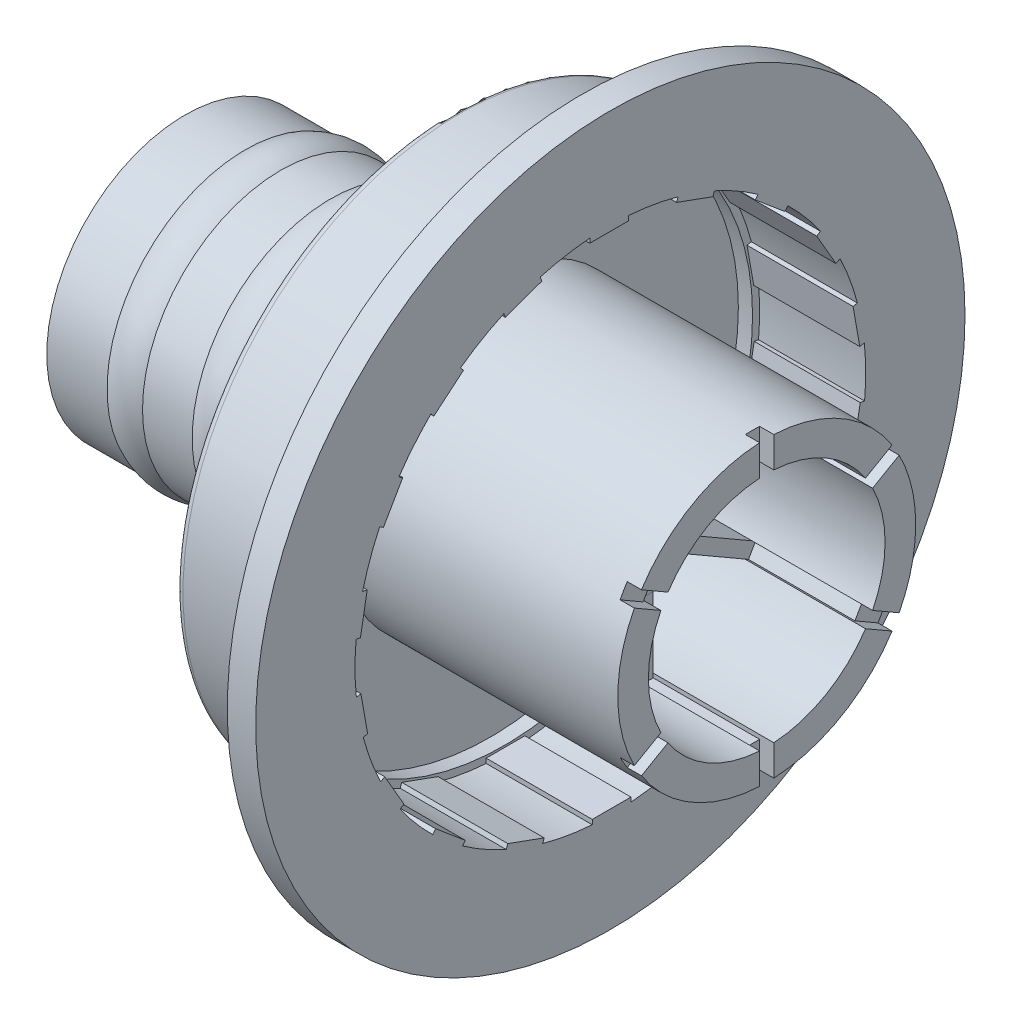
SolidWorks part; units mm, degrees
material "PE High Density"
ref_plane "Front Plane" through (0, 0, 0) normal (0, 0, 1) x (1, 0, 0)
ref_plane "Top Plane" through (0, 0, 0) normal (0, 1, 0) x (1, 0, 0)
ref_plane "Right Plane" through (0, 0, 0) normal (1, 0, 0) x (0, 0, -1)
sketch "Sketch1" plane through (0, 0, 0) normal (0, 0, 1) x (1, 0, 0)
  line L0 (-11.1655, 0) -> (0, 0) construction
  line L2 (0, 5.334) -> (9.906, 5.334)
  line L6 (5.5998, 12.7) -> (6.6158, 12.7)
  line L7 (6.6158, 12.7) -> (6.6158, 9.906)
  line L8 (6.6158, 9.906) -> (11.2522, 9.906)
  line L9 (11.2522, 9.906) -> (11.2522, 4.953)
  line L10 (11.2522, 4.953) -> (20.828, 4.953)
  line L13 (5.5998, 12.7) -> (5.5998, 9.144)
  line L14 (5.5998, 9.144) -> (9.906, 9.144)
  line L15 (9.906, 9.144) -> (9.906, 5.334)
  line L16 (0, 5.334) -> (0, 4.2378)
  line L17 (0, 4.2378) -> (6.35, 4.2378)
  line L18 (0, 0) -> (28.3483, 0) construction
  line L19 (6.35, 4.2378) -> (6.35, 0.4603)
  line L20 (6.35, 0.4603) -> (7.5692, 0.4603)
  line L21 (7.5692, 0.4603) -> (7.5692, 4.191)
  line L22 (7.5692, 4.191) -> (20.828, 4.191)
  line L23 (20.828, 4.191) -> (20.828, 4.953)
  point P1 (0, 4.7859)
  point P5 (6.1078, 12.7)
  dimension "D1" = 10.668
  dimension "D2" = 9.906
  dimension "D3" = 25.4
  dimension "D4" = 3.556
  dimension "D5" = 9.906
  dimension "D6" = 1.016
  dimension "D7" = 0.762
  dimension "D8" = 6.35
  dimension "D9" = 9.5758
  dimension "D10" = 13.2588
  dimension "D11" = 20.828
  dimension "D12" = 0.762
revolve "Revolve2" add sketch "Sketch1" angle 360 about L0
fillet "Fillet1" radius 0.254 1 edges at (11.2522, 0, 9.906)
sketch "Sketch3" plane through (0, 0, 0) normal (0, 0, 1) x (1, 0, 0)
  line L0 (-9.4589, 0) -> (27.8248, 0) construction
  line L1 (18.669, 4.953) -> (17.399, 4.953)
  line L2 (20.828, -4.953) -> (20.828, 4.953) construction
  line L3 (15.621, 4.953) -> (14.351, 4.953)
  arc A0 (17.399, 4.953) -> (18.669, 4.953) centre (18.034, 3.6026) cw
  arc A1 (14.351, 4.953) -> (15.621, 4.953) centre (14.986, 3.6026) cw
  dimension "D1" = 9.906
  dimension "D2" = 2.159
  dimension "D3" = 1.27
  dimension "D4" = 2
revolve "Revolve3" add sketch "Sketch3" angle 360 about L0
sketch "Sketch6" plane through (9.906, 0, 0) normal (-1, 0, 0) x (0, 0, 1)
  line L0 (-0.7374, 9.144) -> (0.6478, 9.144)
  line L1 (0.6478, 9.144) -> (0.6478, 8.9554)
  line L2 (0.6478, 8.9554) -> (-0.7374, 8.9554)
  line L3 (-0.7374, 8.9554) -> (-0.7374, 9.144)
  line L4 (3.6717, 8.1937) -> (2.37, 8.6675)
  line L5 (2.37, 8.6675) -> (2.4345, 8.8448)
  line L6 (3.7362, 8.371) -> (3.6717, 8.1937)
  line L7 (2.4345, 8.8448) -> (3.7362, 8.371)
  line L8 (6.2527, 6.4438) -> (5.1915, 7.3342)
  line L9 (5.1915, 7.3342) -> (5.3127, 7.4787)
  line L10 (6.3739, 6.5883) -> (6.2527, 6.4438)
  line L11 (5.3127, 7.4787) -> (6.3739, 6.5883)
  line L12 (8.0795, 3.9167) -> (7.3869, 5.1163)
  line L13 (7.3869, 5.1163) -> (7.5502, 5.2106)
  line L14 (8.2428, 4.011) -> (8.0795, 3.9167)
  line L15 (7.5502, 5.2106) -> (8.2428, 4.011)
  line L16 (8.9318, 0.9171) -> (8.6913, 2.2813)
  line L17 (8.6913, 2.2813) -> (8.877, 2.3141)
  line L18 (9.1176, 0.9499) -> (8.9318, 0.9171)
  line L19 (8.877, 2.3141) -> (9.1176, 0.9499)
  line L20 (8.7068, -2.1931) -> (8.9474, -0.8289)
  line L21 (8.9474, -0.8289) -> (9.1331, -0.8616)
  line L22 (8.8926, -2.2258) -> (8.7068, -2.1931)
  line L23 (9.1331, -0.8616) -> (8.8926, -2.2258)
  line L24 (7.4317, -5.0387) -> (8.1243, -3.839)
  line L25 (8.1243, -3.839) -> (8.2877, -3.9334)
  line L26 (7.595, -5.133) -> (7.4317, -5.0387)
  line L27 (8.2877, -3.9334) -> (7.595, -5.133)
  line L28 (5.2601, -7.2766) -> (6.3213, -6.3862)
  line L29 (6.3213, -6.3862) -> (6.4426, -6.5307)
  line L30 (5.3814, -7.4211) -> (5.2601, -7.2766)
  line L31 (6.4426, -6.5307) -> (5.3814, -7.4211)
  line L32 (2.4542, -8.6369) -> (3.7559, -8.1631)
  line L33 (3.7559, -8.1631) -> (3.8204, -8.3403)
  line L34 (2.5187, -8.8141) -> (2.4542, -8.6369)
  line L35 (3.8204, -8.3403) -> (2.5187, -8.8141)
  line L36 (-0.6478, -8.9554) -> (0.7374, -8.9554)
  line L37 (0.7374, -8.9554) -> (0.7374, -9.144)
  line L38 (-0.6478, -9.144) -> (-0.6478, -8.9554)
  line L39 (0.7374, -9.144) -> (-0.6478, -9.144)
  line L40 (-3.6717, -8.1937) -> (-2.37, -8.6675)
  line L41 (-2.37, -8.6675) -> (-2.4345, -8.8448)
  line L42 (-3.7362, -8.371) -> (-3.6717, -8.1937)
  line L43 (-2.4345, -8.8448) -> (-3.7362, -8.371)
  line L44 (-6.2527, -6.4438) -> (-5.1915, -7.3342)
  line L45 (-5.1915, -7.3342) -> (-5.3127, -7.4787)
  line L46 (-6.3739, -6.5883) -> (-6.2527, -6.4438)
  line L47 (-5.3127, -7.4787) -> (-6.3739, -6.5883)
  line L48 (-8.0795, -3.9167) -> (-7.3869, -5.1163)
  line L49 (-7.3869, -5.1163) -> (-7.5502, -5.2106)
  line L50 (-8.2428, -4.011) -> (-8.0795, -3.9167)
  line L51 (-7.5502, -5.2106) -> (-8.2428, -4.011)
  line L52 (-8.9318, -0.9171) -> (-8.6913, -2.2813)
  line L53 (-8.6913, -2.2813) -> (-8.877, -2.3141)
  line L54 (-9.1176, -0.9499) -> (-8.9318, -0.9171)
  line L55 (-8.877, -2.3141) -> (-9.1176, -0.9499)
  line L56 (-8.7068, 2.1931) -> (-8.9474, 0.8289)
  line L57 (-8.9474, 0.8289) -> (-9.1331, 0.8616)
  line L58 (-8.8926, 2.2258) -> (-8.7068, 2.1931)
  line L59 (-9.1331, 0.8616) -> (-8.8926, 2.2258)
  line L60 (-7.4317, 5.0387) -> (-8.1243, 3.839)
  line L61 (-8.1243, 3.839) -> (-8.2877, 3.9334)
  line L62 (-7.595, 5.133) -> (-7.4317, 5.0387)
  line L63 (-8.2877, 3.9334) -> (-7.595, 5.133)
  line L64 (-5.2601, 7.2766) -> (-6.3213, 6.3862)
  line L65 (-6.3213, 6.3862) -> (-6.4426, 6.5307)
  line L66 (-5.3814, 7.4211) -> (-5.2601, 7.2766)
  line L67 (-6.4426, 6.5307) -> (-5.3814, 7.4211)
  line L68 (-2.4542, 8.6369) -> (-3.7559, 8.1631)
  line L69 (-3.7559, 8.1631) -> (-3.8204, 8.3403)
  line L70 (-2.5187, 8.8141) -> (-2.4542, 8.6369)
  line L71 (-3.8204, 8.3403) -> (-2.5187, 8.8141)
  point P75 (0, 0)
  dimension "D1" = 1.3853
  dimension "D2" = 0.1886
  dimension "D3" = 18
extrude "Boss-Extrude2" add sketch "Sketch6" along normal up to surface (4.3062 mm away) up to face at (5.5998, 0, 9.144)
sketch "Sketch9" plane through (9.906, 0, 0) normal (-1, 0, 0) x (0, 0, 1)
  circle A0 centre (0, 0) radius 9.144 construction
  circle A1 centre (0, 0) radius 9.144
  circle A2 centre (0, 0) radius 8.89
  dimension "D1" = 0.254
extrude "Boss-Extrude3" add sketch "Sketch9" along normal blind 0.508
sketch "Sketch12" plane through (0, 0, 0) normal (0, 0, 1) x (1, 0, 0)
  line L0 (6.35, 0.9358) -> (6.35, 4.2378)
  line L1 (6.35, 4.2378) -> (4.318, 4.2378)
  line L2 (6.35, 4.2378) -> (0, 4.2378) construction
  line L3 (4.318, 4.2378) -> (4.318, 1.6978)
  line L4 (5.08, 0.9358) -> (6.35, 0.9358)
  arc A0 (4.318, 1.6978) -> (5.08, 0.9358) centre (5.08, 1.6978) ccw
  dimension "D1" = 2.032
  dimension "D2" = 2.54
  dimension "D3" = 3.302
extrude "Boss-Extrude5" add sketch "Sketch12" along normal mid plane 0.508
pattern_circular "CirPattern1" count 6 over 360 about axis through (0, 0, 0) along (1, 0, 0) of "Boss-Extrude5"
sketch "Sketch13" plane through (0, 0, 0) normal (-1, 0, 0) x (0, 0, 1)
  line L0 (-0.254, 0.9358) -> (-0.254, 4.2301) construction
  line L1 (-0.254, 4.0563) -> (0.254, 4.0563)
  line L2 (-0.254, 4.0563) -> (-0.254, 4.3783)
  line L3 (-0.254, 4.3783) -> (0.254, 4.3783)
  line L4 (0.254, 4.0563) -> (0.254, 4.3783)
  line L5 (-0.254, 4.0563) -> (0.254, 4.3783) construction
  line L6 (-0.254, 4.3783) -> (0.254, 4.0563) construction
  line L7 (3.3859, 2.2481) -> (3.9187, 1.9692) construction
  line L8 (3.6647, 2.4091) -> (3.6399, 1.8082) construction
  line L9 (3.3859, 2.2481) -> (3.6647, 2.4091)
  line L10 (3.3859, 2.2481) -> (3.6399, 1.8082)
  line L11 (3.6399, 1.8082) -> (3.9187, 1.9692)
  line L12 (3.6647, 2.4091) -> (3.9187, 1.9692)
  line L13 (3.6399, -1.8082) -> (3.6647, -2.4091) construction
  line L14 (3.9187, -1.9692) -> (3.3859, -2.2481) construction
  line L15 (3.6399, -1.8082) -> (3.9187, -1.9692)
  line L16 (3.6399, -1.8082) -> (3.3859, -2.2481)
  line L17 (3.3859, -2.2481) -> (3.6647, -2.4091)
  line L18 (3.9187, -1.9692) -> (3.6647, -2.4091)
  line L19 (0.254, -4.0563) -> (-0.254, -4.3783) construction
  line L20 (0.254, -4.3783) -> (-0.254, -4.0563) construction
  line L21 (0.254, -4.0563) -> (0.254, -4.3783)
  line L22 (0.254, -4.0563) -> (-0.254, -4.0563)
  line L23 (-0.254, -4.0563) -> (-0.254, -4.3783)
  line L24 (0.254, -4.3783) -> (-0.254, -4.3783)
  line L25 (-3.3859, -2.2481) -> (-3.9187, -1.9692) construction
  line L26 (-3.6647, -2.4091) -> (-3.6399, -1.8082) construction
  line L27 (-3.3859, -2.2481) -> (-3.6647, -2.4091)
  line L28 (-3.3859, -2.2481) -> (-3.6399, -1.8082)
  line L29 (-3.6399, -1.8082) -> (-3.9187, -1.9692)
  line L30 (-3.6647, -2.4091) -> (-3.9187, -1.9692)
  line L31 (-3.6399, 1.8082) -> (-3.6647, 2.4091) construction
  line L32 (-3.9187, 1.9692) -> (-3.3859, 2.2481) construction
  line L33 (-3.6399, 1.8082) -> (-3.9187, 1.9692)
  line L34 (-3.6399, 1.8082) -> (-3.3859, 2.2481)
  line L35 (-3.3859, 2.2481) -> (-3.6647, 2.4091)
  line L36 (-3.9187, 1.9692) -> (-3.6647, 2.4091)
  point P4 (0, 4.2173)
  point P14 (3.6523, 2.1087)
  point P19 (3.6523, -2.1087)
  point P24 (0, -4.2173)
  point P29 (-3.6523, -2.1087)
  point P34 (-3.6523, 2.1087)
  point P35 (0, 0)
  dimension "D1" = 6
extrude "Cut-Extrude1" cut sketch "Sketch13" against normal up to vertex (4.318 mm away)
sketch "Sketch15" plane through (0, 0, 0) normal (-1, 0, 0) x (0, 0, 1)
  line L0 (3.5364, 2.335) -> (4.8524, 2.5082) construction
  line L1 (-0.254, 4.2301) -> (0.254, 4.2301)
  line L2 (-0.254, 4.2301) -> (-0.254, 5.4564)
  line L3 (-0.254, 5.4564) -> (0.254, 5.4564)
  line L4 (0.254, 4.2301) -> (0.254, 5.4564)
  line L5 (-0.254, 4.2301) -> (0.254, 5.4564) construction
  line L6 (-0.254, 5.4564) -> (0.254, 4.2301) construction
  line L7 (4.5984, 2.9482) -> (3.7904, 1.8951) construction
  line L8 (3.5364, 2.335) -> (4.5984, 2.9482)
  line L9 (3.5364, 2.335) -> (3.7904, 1.8951)
  line L10 (3.7904, 1.8951) -> (4.8524, 2.5082)
  line L11 (4.5984, 2.9482) -> (4.8524, 2.5082)
  line L12 (3.7904, -1.8951) -> (4.5984, -2.9482) construction
  line L13 (4.8524, -2.5082) -> (3.5364, -2.335) construction
  line L14 (3.7904, -1.8951) -> (4.8524, -2.5082)
  line L15 (3.7904, -1.8951) -> (3.5364, -2.335)
  line L16 (3.5364, -2.335) -> (4.5984, -2.9482)
  line L17 (4.8524, -2.5082) -> (4.5984, -2.9482)
  line L18 (0.254, -4.2301) -> (-0.254, -5.4564) construction
  line L19 (0.254, -5.4564) -> (-0.254, -4.2301) construction
  line L20 (0.254, -4.2301) -> (0.254, -5.4564)
  line L21 (0.254, -4.2301) -> (-0.254, -4.2301)
  line L22 (-0.254, -4.2301) -> (-0.254, -5.4564)
  line L23 (0.254, -5.4564) -> (-0.254, -5.4564)
  line L24 (-3.5364, -2.335) -> (-4.8524, -2.5082) construction
  line L25 (-4.5984, -2.9482) -> (-3.7904, -1.8951) construction
  line L26 (-3.5364, -2.335) -> (-4.5984, -2.9482)
  line L27 (-3.5364, -2.335) -> (-3.7904, -1.8951)
  line L28 (-3.7904, -1.8951) -> (-4.8524, -2.5082)
  line L29 (-4.5984, -2.9482) -> (-4.8524, -2.5082)
  line L30 (-3.7904, 1.8951) -> (-4.5984, 2.9482) construction
  line L31 (-4.8524, 2.5082) -> (-3.5364, 2.335) construction
  line L32 (-3.7904, 1.8951) -> (-4.8524, 2.5082)
  line L33 (-3.7904, 1.8951) -> (-3.5364, 2.335)
  line L34 (-3.5364, 2.335) -> (-4.5984, 2.9482)
  line L35 (-4.8524, 2.5082) -> (-4.5984, 2.9482)
  point P4 (0, 4.8433)
  point P12 (4.1944, 2.4216)
  point P17 (4.1944, -2.4216)
  point P22 (0, -4.8433)
  point P27 (-4.1944, -2.4216)
  point P32 (-4.1944, 2.4216)
  point P33 (0, 0)
  dimension "D1" = 6
extrude "Cut-Extrude2" cut sketch "Sketch15" against normal blind 0.508
move or copy body "Body-Move/Copy1" bodies to move or copy 110 copy no rotation origin (10.414, 0, 0) rotation axis (0, 1, 0) rotation angle 180
